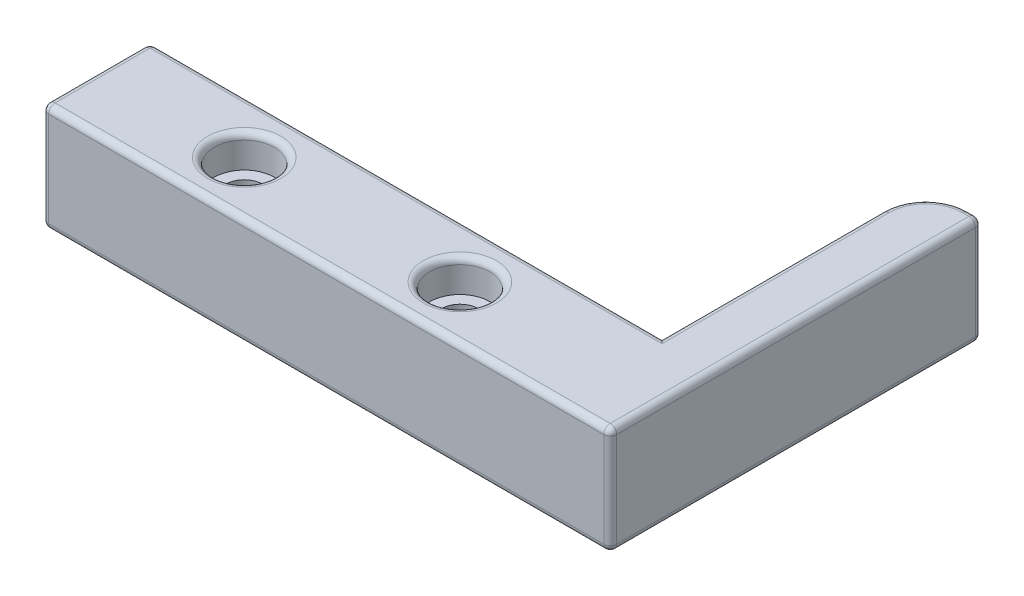
SolidWorks part; units mm, degrees
ref_plane "Front Plane" through (0, 0, 0) normal (0, 0, 1) x (1, 0, 0)
ref_plane "Top Plane" through (0, 0, 0) normal (0, 1, 0) x (1, 0, 0)
ref_plane "Right Plane" through (0, 0, 0) normal (1, 0, 0) x (0, 0, -1)
sketch "Sketch1" plane through (0, 0, 0) normal (0, 1, 0) x (1, 0, 0)
  line L0 (30.1625, 12.7) -> (30.1625, 0) construction
  line L1 (0, 12.7) -> (60.325, 12.7)
  line L2 (0, 12.7) -> (0, 0)
  line L3 (0, 0) -> (60.325, 0)
  line L4 (60.325, 12.7) -> (60.325, 0)
  line L5 (17.4625, 6.35) -> (42.8625, 6.35) construction
  circle A0 centre (17.4625, 6.35) radius 2.159
  circle A1 centre (42.8625, 6.35) radius 2.159
  point P9 (30.1625, 6.35)
  dimension "D3" = 4.318
  dimension "D1" = 12.7
  dimension "D2" = 60.325
  dimension "D4" = 25.4
extrude "Boss-Extrude1" add sketch "Sketch1" along normal blind 12.7
sketch "Sketch5" plane through (60.325, 0, 0) normal (1, 0, 0) x (0, 0, -1)
  line L0 (0, 12.7) -> (12.7, 12.7) construction
  line L1 (0, 12.7) -> (43.7753, 12.7)
  line L2 (0, 12.7) -> (0, 0)
  line L3 (0, 0) -> (43.7753, 0)
  line L4 (43.7753, 12.7) -> (43.7753, 0)
  line L5 (0, 12.7) -> (0, 0) construction
  line L6 (0, 0) -> (12.7, 0) construction
  dimension "D1" = 43.7753
extrude "Boss-Extrude3" add sketch "Sketch5" along normal blind 6.604
sketch "Sketch6" plane through (0, 12.7, 0) normal (0, 1, 0) x (1, 0, 0)
  circle A0 centre (42.8625, 6.35) radius 3.556
  circle A1 centre (17.4625, 6.35) radius 3.556
  circle A2 centre (42.8625, 6.35) radius 2.159 construction
  circle A3 centre (17.4625, 6.35) radius 2.159 construction
  dimension "D1" = 7.112
extrude "Cut-Extrude1" cut sketch "Sketch6" against normal blind 3.81
fillet "Fillet2" radius 5.08 1 edges at (60.325, 6.35, -43.7753)
fillet "Fillet3" radius 0.762 20 edges at (66.167, 12.7, -43.7753) (61.8129, 12.7, -42.2874) (0, 6.35, 0) (0, 6.35, -12.7) (30.1625, 12.7, -12.7) (0, 12.7, -6.35) (33.4645, 12.7, 0) (66.929, 12.7, -21.8876) (60.325, 12.7, -25.6976) (66.929, 6.35, 0) (66.167, 0, -43.7753) (61.8129, 0, -42.2874) (0, 0, -6.35) (30.1625, 0, -12.7) (60.325, 0, -25.6976) (66.929, 0, -21.8876) (33.4645, 0, 0) (66.929, 6.35, -43.7753) (17.4625, 12.7, -2.794) (42.8625, 12.7, -2.794)
